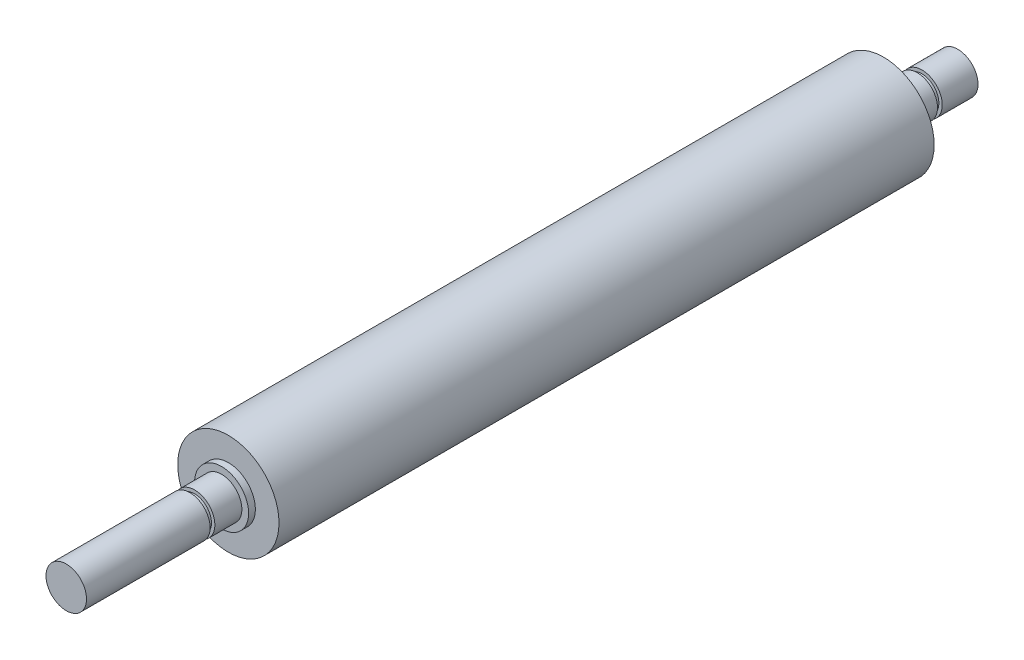
SolidWorks part; units mm, degrees
ref_plane "前视基准面" through (0, 0, 0) normal (0, 0, 1) x (1, 0, 0)
ref_plane "上视基准面" through (0, 0, 0) normal (0, 1, 0) x (1, 0, 0)
ref_plane "右视基准面" through (0, 0, 0) normal (1, 0, 0) x (0, 0, -1)
sketch "草图1" plane through (0, 0, 0) normal (0, 0, 1) x (1, 0, 0)
  circle A0 centre (0, 0) radius 7.5
  dimension "D1" = 15
extrude "凸台-拉伸1" add sketch "草图1" along normal blind 97
sketch "草图2" plane through (0, 0, 0) normal (0, 0, -1) x (-1, 0, 0)
  circle A0 centre (0, 0) radius 4
  dimension "D1" = 8
extrude "凸台-拉伸2" add sketch "草图2" along normal blind 1
sketch "草图3" plane through (0, 0, -1) normal (0, 0, -1) x (-1, 0, 0)
  circle A0 centre (0, 0) radius 3
  dimension "D1" = 6
extrude "凸台-拉伸3" add sketch "草图3" along normal blind 10
sketch "草图4" plane through (0, 0, 97) normal (0, 0, 1) x (1, 0, 0)
  circle A0 centre (0, 0) radius 4
  dimension "D1" = 8
extrude "凸台-拉伸4" add sketch "草图4" along normal blind 1
sketch "草图5" plane through (0, 0, 98) normal (0, 0, 1) x (1, 0, 0)
  circle A0 centre (0, 0) radius 3
  dimension "D1" = 6
extrude "凸台-拉伸5" add sketch "草图5" along normal blind 23
ref_plane "基准面1" through (0, 0, -5) normal (0, 0, -1) x (-1, 0, 0)
sketch "草图6" plane through (0, 0, -5) normal (0, 0, -1) x (-1, 0, 0)
  circle A0 centre (0, 0) radius 6.1471
  circle A1 centre (0, 0) radius 2.5
  dimension "D1" = 5
extrude "切除-拉伸1" cut sketch "草图6" along normal blind 0.7
ref_plane "基准面2" through (0, 0, 102) normal (0, 0, -1) x (-1, 0, 0)
sketch "草图7" plane through (0, 0, 102) normal (0, 0, -1) x (-1, 0, 0)
  circle A0 centre (0, 0) radius 6.1019
  circle A1 centre (0, 0) radius 2.5
  dimension "D1" = 5
extrude "切除-拉伸2" cut sketch "草图7" against normal blind 0.7
